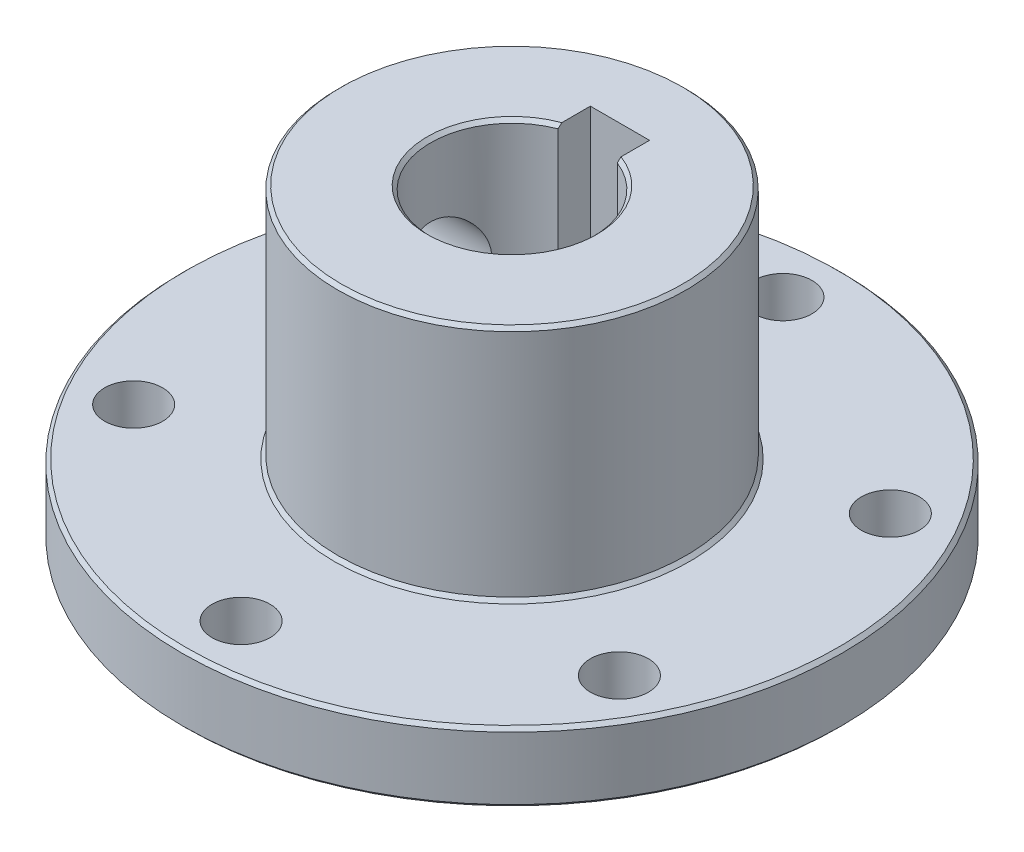
SolidWorks part; units mm, degrees
material "Acier non allié"
ref_plane "Plan de face" through (0, 0, 0) normal (0, 0, 1) x (1, 0, 0)
ref_plane "Plan de dessus" through (0, 0, 0) normal (0, 1, 0) x (1, 0, 0)
ref_plane "Plan de droite" through (0, 0, 0) normal (1, 0, 0) x (0, 0, -1)
sketch "Esquisse1" plane through (0, 0, 0) normal (0, 1, 0) x (1, 0, 0)
  circle A0 centre (0, 0) radius 28.4
  circle A1 centre (0, 0) radius 7
  dimension "D1" = 56.8
  dimension "D2" = 14
extrude "Boss.-Extru.1" add sketch "Esquisse1" along normal blind 26.4
sketch "Esquisse2" plane through (0, 26.4, 0) normal (0, 1, 0) x (1, 0, 0)
  circle A0 centre (0, 0) radius 15
  dimension "D1" = 30
extrude "Enlèv. mat.-Extru.1" cut sketch "Esquisse2" against normal offset from surface (20.4 mm away) 6 flip side to cut up to face at (0, 0, 28.4)
sketch "Esquisse3" plane through (0, 0, 0) normal (0, -1, 0) x (1, 0, 0)
  circle A0 centre (0, 0) radius 23.75 construction
  circle A1 centre (0.4093, 23.7465) radius 2.5
  circle A2 centre (20.7697, 11.5188) radius 2.5
  circle A3 centre (20.3604, -12.2277) radius 2.5
  circle A4 centre (-0.4093, -23.7465) radius 2.5
  circle A5 centre (-20.7697, -11.5188) radius 2.5
  circle A6 centre (-20.3604, 12.2277) radius 2.5
  dimension "D1" = 47.5
  dimension "D3" = 5
  dimension "D2" = 6
extrude "Enlèv. mat.-Extru.2" cut sketch "Esquisse3" against normal through all
sketch "Esquisse4" plane through (0, 0, 0) normal (1, 0, 0) x (0, 0, -1)
  line L0 (0, 26.4) -> (0, 0) construction
  line L1 (15, 26.4) -> (-15, 26.4) construction
  line L2 (-28.4, 0) -> (28.4, 0) construction
  circle A0 centre (0, 16.2) radius 4
  dimension "D2" = 8
  dimension "D1" = 10.2
extrude "Enlèv. mat.-Extru.3" cut sketch "Esquisse4" against normal up to surface (14.4568 mm away)
sketch "Esquisse5" plane through (0, 26.4, 0) normal (0, 1, 0) x (1, 0, 0)
  line L0 (0, 4.65) -> (0, 0) construction
  line L1 (2.55, 0) -> (-2.55, 0)
  line L2 (2.55, 0) -> (2.55, 9.3)
  line L3 (2.55, 9.3) -> (-2.55, 9.3)
  line L4 (-2.55, 0) -> (-2.55, 9.3)
  line L5 (2.55, 0) -> (-2.55, 9.3) construction
  line L6 (2.55, 9.3) -> (-2.55, 0) construction
  point P0 (0, 4.65)
  point P8 (2.5, -3.7277)
  dimension "D1" = 5.1
  dimension "D2" = 9.3
extrude "Enlèv. mat.-Extru.4" cut sketch "Esquisse5" against normal through all
chamfer "Chanfrein1" distance 0.3 angle 45 6 edges at (0, 26.4, 15) (0, 6, 28.4) (0, 0, 28.4) (0, 6, 15) (0, 0, 7) (0, 26.4, 7)
